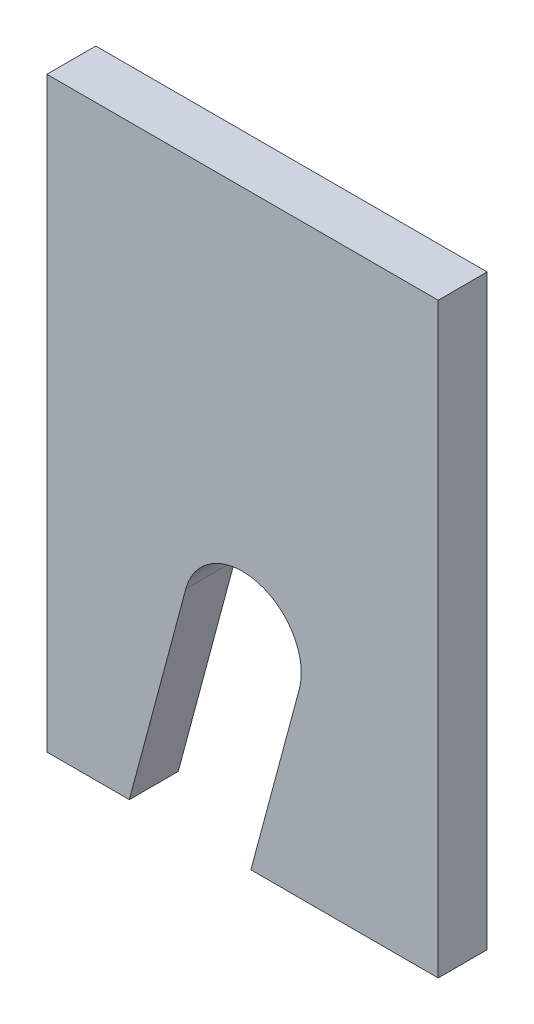
SolidWorks part; units mm, degrees
ref_plane "Front Plane" through (0, 0, 0) normal (0, 0, 1) x (1, 0, 0)
ref_plane "Top Plane" through (0, 0, 0) normal (0, 1, 0) x (1, 0, 0)
ref_plane "Right Plane" through (0, 0, 0) normal (1, 0, 0) x (0, 0, -1)
sketch "Sketch1" plane through (0, 0, 0) normal (0, 0, 1) x (1, 0, 0)
  line L5 (18.0396, 27.3722) -> (10.7053, 0)
  line L6 (0, 0) -> (10.7053, 0)
  line L10 (0, 0) -> (0, 76.2)
  line L11 (0, 76.2) -> (50.8, 76.2)
  line L12 (50.8, 0) -> (50.8, 76.2)
  line L13 (25.4, 76.2) -> (25.4, 0) construction
  line L14 (0, 38.1) -> (50.8, 38.1) construction
  line L15 (32.7604, 23.4278) -> (26.4829, 0)
  line L16 (25.4, 0) -> (50.8, 0)
  arc A0 (32.7604, 23.4278) -> (18.0396, 27.3722) centre (25.4, 25.4) ccw
  point P149 (25.4, 38.1)
  dimension "D3" = 50.8
  dimension "D2" = 15.24
  dimension "D1" = 50.8
  dimension "D4" = 105
  dimension "4" = 76.2
extrude "Boss-Extrude1" add sketch "Sketch1" along normal blind 6.35 contours A0 L15 L16 L12 L11 L10 L6 L5
sketch "Sketch2" plane through (0, 0, 6.35) normal (0, 0, 1) x (1, 0, 0)
  line L0 (0, 76.2) -> (50.8, 76.2) construction
  line L1 (12.7, 76.2) -> (38.1, 76.2)
  line L2 (12.7, 76.2) -> (12.7, 38.1)
  line L3 (12.7, 38.1) -> (38.1, 38.1)
  line L4 (38.1, 76.2) -> (38.1, 38.1)
  line L5 (25.4, 38.1) -> (25.4, 76.2) construction
  line L6 (12.7, 57.15) -> (38.1, 57.15) construction
  point P6 (0, 0)
  point P268 (25.4, 57.15)
  dimension "D1" = 25.4
  dimension "D2" = 38.1
